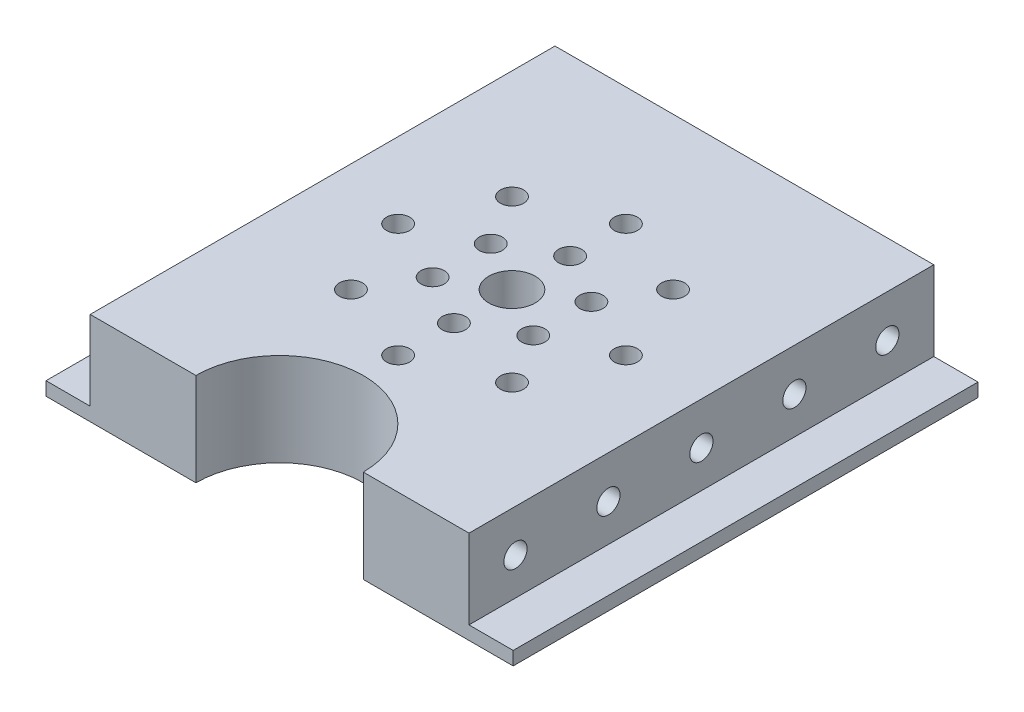
SolidWorks part; units mm, degrees
material "PVC rigide"
ref_plane "Plan de face" through (0, 0, 0) normal (0, 0, 1) x (1, 0, 0)
ref_plane "Plan de dessus" through (0, 0, 0) normal (0, 1, 0) x (1, 0, 0)
ref_plane "Plan de droite" through (0, 0, 0) normal (1, 0, 0) x (0, 0, -1)
sketch "Esquisse1" plane through (0, 0, 0) normal (0, 1, 0) x (1, 0, 0)
  line L1 (50.25, 50) -> (-50.25, 50)
  line L2 (50.25, 50) -> (50.25, -50)
  line L3 (50.25, -50) -> (-50.25, -50)
  line L4 (-50.25, 50) -> (-50.25, -50)
  line L5 (50.25, 50) -> (-50.25, -50) construction
  line L6 (50.25, -50) -> (-50.25, 50) construction
  point P0 (0, 0)
  dimension "D1" = 100.5
  dimension "D2" = 100
extrude "Boss.-Extru.1" add sketch "Esquisse1" along normal blind 20
sketch "Esquisse2" plane through (0, 20, 0) normal (0, 1, 0) x (1, 0, 0)
  line L0 (50.25, 50) -> (-50.25, 50) construction
  line L1 (50.25, -50) -> (40.75, -50)
  line L2 (50.25, -50) -> (50.25, 50)
  line L3 (50.25, 50) -> (40.75, 50)
  line L4 (40.75, -50) -> (40.75, 50)
  line L6 (-40.75, 50) -> (-50.25, 50)
  line L7 (-40.75, 50) -> (-40.75, -50)
  line L8 (-40.75, -50) -> (-50.25, -50)
  line L9 (-50.25, 50) -> (-50.25, -50)
  dimension "D1" = 9.5
extrude "Enlèv. mat.-Extru.1" cut sketch "Esquisse2" against normal offset from surface (17.1 mm away) 2.9 up to face at (0, 0, 0)
sketch "Esquisse3" plane through (-40.75, 0, 0) normal (-1, 0, 0) x (0, 0, 1)
  line L0 (-50, 10.9) -> (50, 10.9) construction
  line L1 (-50, 2.9) -> (-50, 20) construction
  line L2 (50, 2.9) -> (50, 20) construction
  line L3 (50, 2.9) -> (-50, 2.9) construction
  line L4 (0, 0) -> (0, 20) construction
  line L5 (50, 20) -> (-50, 20) construction
  circle A0 centre (-40, 10.9) radius 2.5
  circle A1 centre (-20, 10.9) radius 2.5
  circle A2 centre (0, 10.9) radius 2.5
  circle A3 centre (20, 10.9) radius 2.5
  circle A4 centre (40, 10.9) radius 2.5
  dimension "D4" = 5
  dimension "D1" = 8
  dimension "D2" = 10
  dimension "D3" = 20
extrude "Enlèv. mat.-Extru.2" cut sketch "Esquisse3" against normal blind 16
sketch "Esquisse4" plane through (40.75, 0, 0) normal (1, 0, 0) x (0, 0, -1)
  circle A1 centre (-20, 10.9) radius 2.5
  circle A2 centre (-20, 10.9) radius 2.5
  circle A3 centre (0, 10.9) radius 2.5
  circle A4 centre (0, 10.9) radius 2.5
  circle A5 centre (20, 10.9) radius 2.5
  circle A6 centre (20, 10.9) radius 2.5
  circle A7 centre (40, 10.9) radius 2.5
  circle A8 centre (40, 10.9) radius 2.5
  circle A9 centre (-40, 10.9) radius 2.5
  circle A10 centre (-40, 10.9) radius 2.5
  dimension "D1" = 0
  dimension "D2" = 0
  dimension "D3" = 0
  dimension "D4" = 0
  dimension "D5" = 0
extrude "Enlèv. mat.-Extru.3" cut sketch "Esquisse4" against normal blind 16
sketch "Esquisse5" plane through (0, 20, 0) normal (0, 1, 0) x (1, 0, 0)
  circle A0 centre (0, 0) radius 24.5 construction
  circle A1 centre (0, -24.5) radius 2.5
  circle A2 centre (-17.3241, -17.3241) radius 2.5
  circle A3 centre (-24.5, 0) radius 2.5
  circle A4 centre (-17.3241, 17.3241) radius 2.5
  circle A5 centre (0, 24.5) radius 2.5
  circle A6 centre (17.3241, 17.3241) radius 2.5
  circle A7 centre (24.5, 0) radius 2.5
  circle A8 centre (17.3241, -17.3241) radius 2.5
  dimension "D1" = 49
  dimension "D2" = 5
  dimension "D3" = 8
extrude "Enlèv. mat.-Extru.4" cut sketch "Esquisse5" against normal through all
sketch "Esquisse6" plane through (0, 20, 0) normal (0, 1, 0) x (1, 0, 0)
  circle A0 centre (0, 0) radius 5
  dimension "D1" = 10
extrude "Enlèv. mat.-Extru.5" cut sketch "Esquisse6" against normal through all
sketch "Esquisse7" plane through (0, 0, 0) normal (0, -1, 0) x (1, 0, 0)
  circle A0 centre (0, 0) radius 30
  dimension "D1" = 60
extrude "Enlèv. mat.-Extru.6" cut sketch "Esquisse7" against normal blind 4
sketch "Esquisse8" plane through (0, 4, 0) normal (0, -1, 0) x (1, 0, 0)
  circle A0 centre (0, 0) radius 19
  dimension "D1" = 38
extrude "Enlèv. mat.-Extru.7" cut sketch "Esquisse8" against normal blind 4
sketch "Esquisse9" plane through (0, 8, 0) normal (0, -1, 0) x (1, 0, 0)
  circle A0 centre (0, 0) radius 12.5 construction
  circle A1 centre (0, -12.5) radius 2.5
  circle A2 centre (-10.8253, -6.25) radius 2.5
  circle A3 centre (-10.8253, 6.25) radius 2.5
  circle A4 centre (0, 12.5) radius 2.5
  circle A5 centre (10.8253, 6.25) radius 2.5
  circle A6 centre (10.8253, -6.25) radius 2.5
  dimension "D1" = 25
  dimension "D2" = 5
  dimension "D3" = 6
extrude "Enlèv. mat.-Extru.8" cut sketch "Esquisse9" against normal through all
sketch "Esquisse11" plane through (0, 20, 0) normal (0, 1, 0) x (1, 0, 0)
  line L0 (-40.75, -50) -> (40.75, -50) construction
  circle A0 centre (0, -50) radius 18
  dimension "D1" = 36
extrude "Enlèv. mat.-Extru.9" cut sketch "Esquisse11" against normal through all
